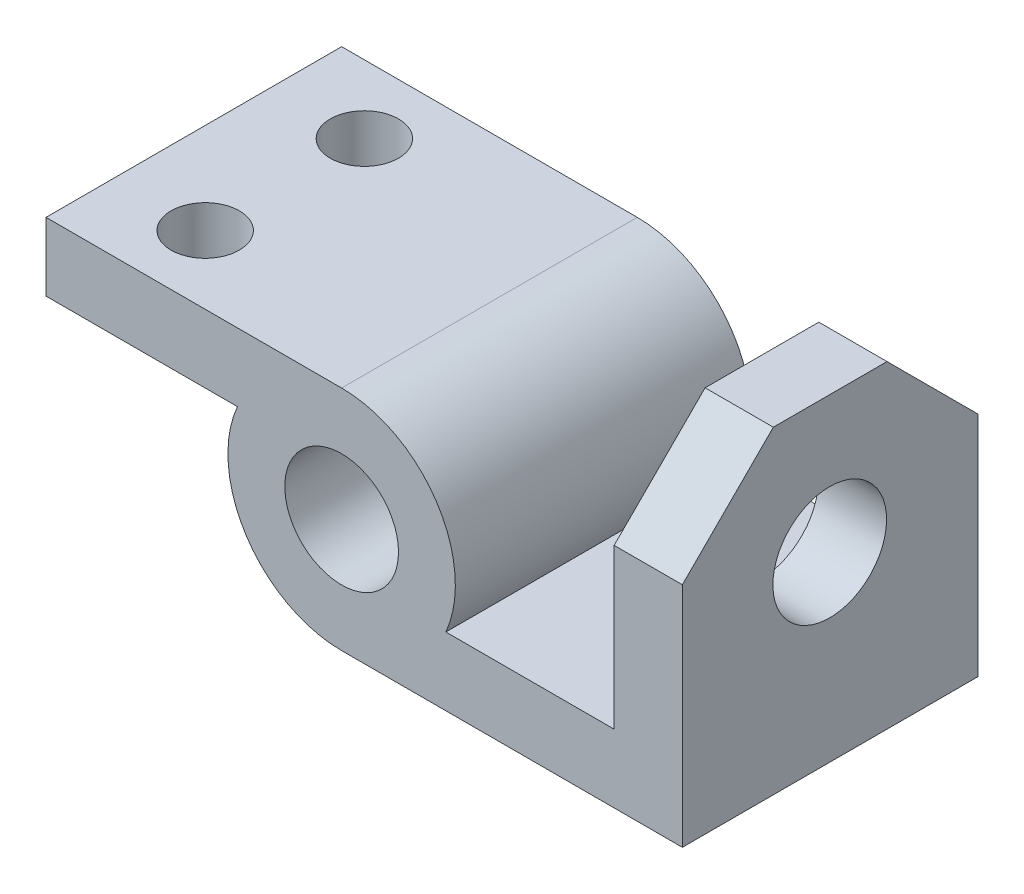
SolidWorks part; units mm, degrees
ref_plane "Front Plane" through (0, 0, 0) normal (0, 0, 1) x (1, 0, 0)
ref_plane "Top Plane" through (0, 0, 0) normal (0, 1, 0) x (1, 0, 0)
ref_plane "Right Plane" through (0, 0, 0) normal (1, 0, 0) x (0, 0, -1)
sketch "Sketch1" plane through (0, 0, 0) normal (0, 0, 1) x (1, 0, 0)
  line L0 (0, 12.5) -> (-32.5, 12.5)
  line L1 (-32.5, 12.5) -> (-32.5, 5)
  line L2 (-32.5, 5) -> (-11.4564, 5)
  line L3 (-0.0435, -12.4999) -> (37.4565, -12.4999)
  line L5 (29.9565, -4.9999) -> (11.4565, -4.9999)
  line L6 (29.9565, -4.9999) -> (29.9565, 22.5001)
  line L7 (29.9565, 22.5001) -> (37.4565, 22.5001)
  line L8 (37.4565, 22.5001) -> (37.4565, -12.4999)
  circle A0 centre (0, 0) radius 6.25
  arc A3 (0, 12.5) -> (11.4565, -4.9999) centre (0, 0) cw
  arc A4 (-0.0435, -12.4999) -> (-11.4564, 5) centre (0, 0) cw
  point P4 (10.4802, -5.0736)
  point P6 (20.7065, -4.9999)
  point P8 (0.7715, -12.5)
  point P9 (0, 0)
  point P18 (0, 0)
  point P19 (15.8965, 12.5)
  point P21 (-13.4637, 0.2646)
  point P25 (1.0635, 12.4547)
  point P26 (0, 0)
  point P27 (0, 0)
  dimension "D1" = 12.5
  dimension "D2" = 7.5
  dimension "D7" = 12.5
  dimension "D8" = 12.5
  dimension "D10" = 37.5
  dimension "D3" = 7.5
  dimension "D4" = 18.5
  dimension "D5" = 7.5
  dimension "D6" = 35
  dimension "D9" = 32.5
extrude "Boss-Extrude1" add sketch "Sketch1" along normal blind 32.5
sketch "Sketch2" plane through (0, 12.5, 0) normal (0, 1, 0) x (1, 0, 0)
  line L0 (0, 0) -> (-32.5, 0) construction
  line L1 (-32.5, -32.5) -> (-32.5, 0) construction
  line L2 (-32.5, -16.25) -> (0, -16.25) construction
  line L3 (0, -32.5) -> (0, 0) construction
  circle A0 centre (-22.5, -7.5) radius 3.75
  circle A1 centre (-22.5, -25) radius 3.75
  dimension "D1" = 7.5
  dimension "D2" = 7.5
  dimension "D3" = 10
extrude "Cut-Extrude1" cut sketch "Sketch2" against normal through all and the other way through all
sketch "Sketch3" plane through (37.4565, 0, 0) normal (1, 0, 0) x (0, 0, -1)
  line L0 (0, -12.4999) -> (0, 22.5001) construction
  line L2 (-32.5, -12.4999) -> (0, -12.4999) construction
  circle A0 centre (-16.3, 7.5001) radius 6.25
  point P4 (0, 0)
  point P6 (-15.2788, 13.5858)
  point P7 (-15.7045, 13.231)
  dimension "D1" = 12.5
  dimension "D2" = 16.3
  dimension "D3" = 20
extrude "Cut-Extrude2" cut sketch "Sketch3" against normal up to next
chamfer "Chamfer1" distance 10 2 edges at (33.7065, 22.5001, 0) (33.7065, 22.5001, 32.5)
